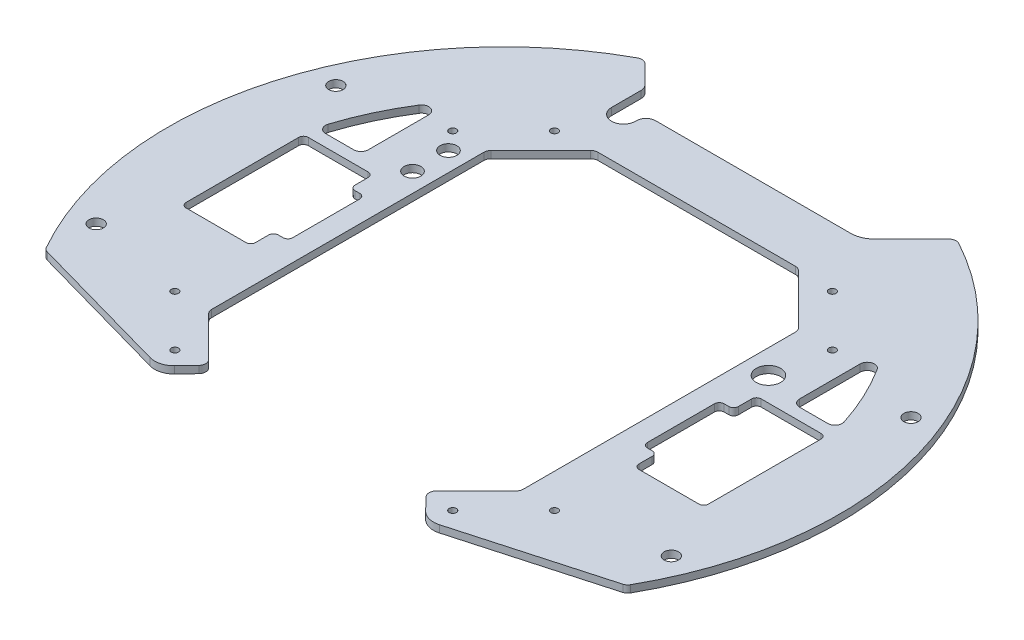
SolidWorks part; units mm, degrees
material "1060 Alloy"
ref_plane "Front Plane" through (0, 0, 0) normal (0, 0, 1) x (1, 0, 0)
ref_plane "Top Plane" through (0, 0, 0) normal (0, 1, 0) x (1, 0, 0)
ref_plane "Right Plane" through (0, 0, 0) normal (1, 0, 0) x (0, 0, -1)
sketch "Sketch1" plane through (0, 0, 0) normal (0, 1, 0) x (1, 0, 0)
  circle A0 centre (0, 0) radius 140
  dimension "D1" = 280
extrude "Boss-Extrude1" add sketch "Sketch1" along normal blind 3
sketch "Sketch17" plane through (0, 0, 0) normal (0, -1, 0) x (1, 0, 0)
  line L0 (-50, 90) -> (-121.2436, 70)
  line L1 (-50, 90) -> (50, 90)
  line L2 (-121.2436, 70) -> (-121.2436, 140)
  line L3 (-121.2436, 140) -> (121.2436, 140)
  line L4 (121.2436, 140) -> (121.2436, 70)
  line L5 (121.2436, 70) -> (50, 90)
  circle A0 centre (0, 0) radius 140 construction
  dimension "D1" = 90
  dimension "D2" = 50
  dimension "D3" = 50
  dimension "D4" = 70
extrude "Cut-Extrude1" cut sketch "Sketch17" against normal up to next
sketch "Sketch19" plane through (0, 3, 0) normal (0, 1, 0) x (1, 0, 0)
  line L0 (-68.5894, 68.5894) -> (68.5894, -68.5894) construction
  line L1 (97, 40.1787) -> (40.1787, 97) construction
  line L2 (40.1787, 97) -> (-40.1787, 97) construction
  line L3 (-40.1787, 97) -> (-97, 40.1787) construction
  line L4 (-97, 40.1787) -> (-97, -40.1787) construction
  line L5 (-97, -40.1787) -> (-40.1787, -97) construction
  line L6 (-40.1787, -97) -> (40.1787, -97) construction
  line L7 (40.1787, -97) -> (97, -40.1787) construction
  line L8 (97, -40.1787) -> (97, 40.1787) construction
  line L9 (68.5894, 68.5894) -> (-68.5894, -68.5894) construction
  circle A0 centre (-79.196, -57.9828) radius 1.5
  circle A1 centre (-79.196, 57.9828) radius 1.5
  circle A2 centre (79.196, 57.9828) radius 1.5
  circle A3 centre (79.196, -57.9828) radius 1.5
  circle A4 centre (0, 0) radius 97 construction
  circle A5 centre (-57.9828, -79.196) radius 1.5
  circle A6 centre (57.9828, 79.196) radius 1.5
  circle A7 centre (-57.9828, 79.196) radius 1.5
  circle A8 centre (57.9828, -79.196) radius 1.5
  dimension "D5" = 3
  dimension "D1" = 15
  dimension "D2" = 15
  dimension "D6" = 97
extrude "Cut-Extrude3" cut sketch "Sketch19" against normal up to next
sketch "Sketch20" plane through (0, 3, 0) normal (0, 1, 0) x (1, 0, 0)
  line L0 (-65, 123.996) -> (-45, 103.996)
  line L1 (-45, 103.996) -> (45, 103.996)
  line L2 (45, 103.996) -> (65, 123.996)
  arc A1 (121.2436, -70) -> (-121.2436, -70) centre (0, 0) ccw construction
  dimension "D1" = 130
  dimension "D2" = 90
  dimension "D3" = 45
extrude "Cut-Extrude4" cut sketch "Sketch20" against normal up to next
sketch "Sketch21" plane through (0, 3, 0) normal (0, 1, 0) x (1, 0, 0)
  line L0 (-42.4669, 80.5696) -> (0, 60)
  line L1 (0, 60) -> (42.4669, 80.5696)
  line L2 (59.9558, 63.0807) -> (40, 15)
  line L3 (40, 15) -> (61.3906, -61.646)
  line L4 (52.194, -84.7177) -> (0, -30) construction
  line L5 (0, -30) -> (-52.194, -84.7177) construction
  line L6 (-61.3906, -61.646) -> (-40, 15)
  line L7 (-40, 15) -> (-59.9558, 63.0807)
  line L8 (-59.9558, 63.0807) -> (-42.4669, 80.5696)
  line L9 (42.4669, 80.5696) -> (59.9558, 63.0807)
  line L10 (-45.4202, -77.6164) -> (-52.3849, -84.9179)
  line L12 (-68.5894, 68.5894) -> (68.5894, -68.5894) construction
  line L13 (97, 40.1787) -> (40.1787, 97) construction
  line L14 (40.1787, 97) -> (-40.1787, 97) construction
  line L15 (-40.1787, 97) -> (-97, 40.1787) construction
  line L16 (-97, 40.1787) -> (-97, -40.1787) construction
  line L17 (-97, -40.1787) -> (-40.1787, -97) construction
  line L18 (-40.1787, -97) -> (40.1787, -97) construction
  line L19 (40.1787, -97) -> (97, -40.1787) construction
  line L20 (97, -40.1787) -> (97, 40.1787) construction
  line L21 (68.5894, 68.5894) -> (-68.5894, -68.5894) construction
  line L22 (-45.4202, -77.6164) -> (-61.3906, -61.646)
  line L23 (-121.2436, -70) -> (-50, -90) construction
  line L24 (-60.336, -87.0984) -> (-50, -90)
  line L25 (45.4202, -77.6164) -> (61.3906, -61.646)
  line L26 (-59.9558, 63.0807) -> (-65.3716, 76.1292) construction
  line L27 (-54.4954, 86.3958) -> (-42.4669, 80.5696) construction
  line L28 (42.4669, 80.5696) -> (54.4954, 86.3958) construction
  line L29 (65.3716, 76.1292) -> (59.9558, 63.0807) construction
  line L30 (-50, -90) -> (50, -90)
  line L31 (50, -90) -> (60.336, -87.0984)
  line L32 (50, -90) -> (121.2436, -70) construction
  line L34 (52.3849, -84.9179) -> (45.4202, -77.6164)
  arc A0 (-65.3716, 76.1292) -> (-54.4954, 86.3958) centre (-57.9828, 79.196) cw construction
  arc A1 (54.4954, 86.3958) -> (65.3716, 76.1292) centre (57.9828, 79.196) cw construction
  arc A2 (-52.194, -84.7177) -> (-65.6416, -76.8845) centre (-57.9828, -79.196) cw construction
  arc A3 (65.6416, -76.8845) -> (52.194, -84.7177) centre (57.9828, -79.196) cw construction
  arc A4 (-52.3849, -84.9179) -> (-60.336, -87.0984) centre (-58.1737, -79.3962) cw
  circle A5 centre (0, 0) radius 97 construction
  arc A6 (52.3849, -84.9179) -> (60.336, -87.0984) centre (58.1737, -79.3962) ccw
  ellipse E0 centre (0, 15) end of major axis (0, 60) minor radius 40 construction
  dimension "D1" = 40
  dimension "D2" = 8
  dimension "D3" = 15
  dimension "D4" = 15
  dimension "D5" = 45
  dimension "D6" = 10
  dimension "D7" = 10
  dimension "D8" = 97
  dimension "D9" = 10
  dimension "D14" = 10
extrude "Cut-Extrude5" cut sketch "Sketch21" against normal up to next
fillet "Fillet1" radius 20 3 edges at (40, 1.5, -15) (-40, 1.5, -15) (0, 1.5, -60)
fillet "Fillet2" radius 10 2 edges at (45, 1.5, -103.996) (-45, 1.5, -103.996)
sketch "Sketch22" plane through (0, 3, 0) normal (0, 1, 0) x (1, 0, 0)
  line L1 (80, 25.5) -> (109, 25.5)
  line L2 (80, 25.5) -> (80, -25.5)
  line L3 (80, -25.5) -> (109, -25.5)
  line L4 (109, 25.5) -> (109, -25.5)
  line L5 (-109, 25.5) -> (-80, 25.5)
  line L6 (-109, 25.5) -> (-109, -25.5)
  line L7 (-109, -25.5) -> (-80, -25.5)
  line L8 (-80, 25.5) -> (-80, -25.5)
  dimension "D1" = 80
  dimension "D2" = 80
  dimension "D4" = 51
  dimension "D5" = 29
  dimension "D7" = 25.5
extrude "Cut-Extrude6" cut sketch "Sketch22" against normal up to next
sketch "Sketch31" plane through (0, 3, 0) normal (0, 1, 0) x (1, 0, 0)
  line L0 (-80, -25.5) -> (-80, 25.5) construction
  line L1 (-80, 16) -> (-74, 16)
  line L2 (-80, 16) -> (-80, -16)
  line L3 (-80, -16) -> (-74, -16)
  line L4 (-74, 16) -> (-74, -16)
  line L5 (80, 25.5) -> (80, -25.5) construction
  line L6 (80, 16) -> (74, 16)
  line L7 (80, 16) -> (80, -16)
  line L8 (80, -16) -> (74, -16)
  line L9 (74, 16) -> (74, -16)
  line L10 (-109, 25.5) -> (-109, -25.5) construction
  dimension "D1" = 32
  dimension "D2" = 35
  dimension "D3" = 16
extrude "Cut-Extrude15" cut sketch "Sketch31" against normal up to next
fillet "Fillet3" radius 2 16 edges at (109, 1.5, 25.5) (80, 1.5, 25.5) (80, 1.5, -25.5) (109, 1.5, -25.5) (-80, 1.5, 25.5) (-109, 1.5, 25.5) (-80, 1.5, -25.5) (-109, 1.5, -25.5) (80, 1.5, 16) (74, 1.5, 16) (74, 1.5, -16) (80, 1.5, -16) (-80, 1.5, 16) (-74, 1.5, 16) (-80, 1.5, -16) (-74, 1.5, -16)
sketch "Sketch23" plane through (0, 3, 0) normal (0, 1, 0) x (1, 0, 0)
  circle A0 centre (-120, 50) radius 3
  circle A1 centre (-120, -50) radius 3
  circle A2 centre (120, -50) radius 3
  circle A3 centre (120, 50) radius 3
  dimension "D1" = 6
  dimension "D2" = 120
  dimension "D3" = 120
  dimension "D4" = 50
  dimension "D5" = 50
extrude "Cut-Extrude7" cut sketch "Sketch23" against normal up to next
sketch "Sketch24" plane through (0, 3, 0) normal (0, 1, 0) x (1, 0, 0)
  line L0 (-90, 68.3301) -> (-90, 30.5)
  line L1 (-90, 30.5) -> (-108.806, 30.5)
  line L2 (-82, 25.5) -> (-107, 25.5) construction
  arc A0 (-108.806, 30.5) -> (-90, 68.3301) centre (0, 0) cw
  arc A2 (-65, 123.996) -> (-121.2436, -70) centre (0, 0) ccw construction
  dimension "D3" = 27
  dimension "D1" = 5
  dimension "D2" = 90
extrude "Cut-Extrude8" cut sketch "Sketch24" against normal up to next (3 mm away)
fillet "Fillet4" radius 3 3 edges at (-90, 1.5, -68.3301) (-90, 1.5, -30.5) (-108.806, 1.5, -30.5)
mirror "Mirror1" about plane through (0, 0, 0) normal (1, 0, 0) of "Fillet4", "Cut-Extrude8"
sketch "Sketch26" plane through (0, 3, 0) normal (0, 1, 0) x (1, 0, 0)
  line L0 (-59.9558, 63.0807) -> (-65, 58.0366)
  line L1 (-59.9558, 63.0807) -> (-42.65, 21.3847) construction
  line L2 (-65, 58.0366) -> (-65, -58.0366)
  line L3 (-65, -58.0366) -> (-61.3906, -61.646)
  line L5 (-59.9558, 63.0807) -> (59.9558, 63.0807)
  line L6 (42.65, 21.3847) -> (59.9558, 63.0807) construction
  line L7 (59.9558, 63.0807) -> (65, 58.0366)
  line L8 (65, 58.0366) -> (65, -58.0366)
  line L9 (65, -58.0366) -> (61.3906, -61.646)
  line L10 (61.3906, -61.646) -> (41.8582, 8.3417) construction
  line L11 (61.3906, -61.646) -> (-61.3906, -61.646)
  line L12 (-80, -23.5) -> (-80, -18) construction
  line L13 (-41.8582, 8.3417) -> (-61.3906, -61.646) construction
  line L14 (-61.3906, -61.646) -> (-45.4202, -77.6164) construction
  line L15 (-42.4669, 80.5696) -> (-59.9558, 63.0807) construction
  dimension "D1" = 15
extrude "Cut-Extrude10" cut sketch "Sketch26" against normal up to next
sketch "Sketch27" plane through (0, 3, 0) normal (0, 1, 0) x (1, 0, 0)
  line L0 (-42.4669, 80.5696) -> (-65, 58.0366) construction
  line L1 (-42.4669, 80.5696) -> (42.4669, 80.5696)
  line L2 (65, 58.0366) -> (42.4669, 80.5696) construction
  line L3 (-42.4669, 62.2226) -> (42.4669, 62.2226)
  line L5 (-8.7185, 64.223) -> (-42.4669, 80.5696) construction
  line L8 (-42.4669, 62.2226) -> (-42.4669, 80.5696)
  line L9 (42.4669, 62.2226) -> (42.4669, 80.5696)
  arc A0 (-8.7185, 64.223) -> (-5.7955, 63.0807) centre (0, 82.2226) ccw construction
extrude "Cut-Extrude11" cut sketch "Sketch27" against normal up to next
sketch "Sketch28" plane through (0, 3, 0) normal (0, 1, 0) x (1, 0, 0)
  line L0 (-49.55, 99.6) -> (-49.55, 119.6) construction
  line L1 (-54.55, 99.6) -> (-54.55, 119.6)
  line L2 (-44.55, 99.6) -> (-44.55, 119.6)
  arc A0 (-54.55, 99.6) -> (-44.55, 99.6) centre (-49.55, 99.6) ccw
  arc A1 (-44.55, 119.6) -> (-54.55, 119.6) centre (-49.55, 119.6) ccw
  point P2 (-49.55, 109.6)
  dimension "D1" = 5
  dimension "D2" = 49.55
  dimension "D3" = 99.6
  dimension "D4" = 20
extrude "Cut-Extrude12" cut sketch "Sketch28" against normal up to next
fillet "Fillet5" radius 3 12 edges at (-65, 1.5, -123.996) (65, 1.5, -123.996) (121.2436, 1.5, 70) (65, 1.5, 58.0366) (65, 1.5, -58.0366) (-65, 1.5, -58.0366) (-65, 1.5, 58.0366) (-121.2436, 1.5, 70) (45.4202, 1.5, 77.6164) (-45.4202, 1.5, 77.6164) (42.4669, 1.5, -80.5696) (-42.4669, 1.5, -80.5696)
fillet "Fillet6" radius 4 2 edges at (-44.55, 1.5, -104.7025) (-54.55, 1.5, -113.546)
sketch "Sketch29" plane through (0, 3, 0) normal (0, 1, 0) x (1, 0, 0)
  line L0 (65, -56.7939) -> (65, 56.7939) construction
  line L2 (104.7748, 30.5) -> (93, 30.5) construction
  circle A0 centre (75, 35.5) radius 5.1
  dimension "D1" = 10.2
  dimension "D2" = 10
  dimension "D3" = 5
extrude "Cut-Extrude13" cut sketch "Sketch29" against normal up to next
sketch "Sketch30" plane through (0, 3, 0) normal (0, 1, 0) x (1, 0, 0)
  line L1 (-65, 56.7939) -> (-65, -56.7939) construction
  circle A0 centre (-73, 50) radius 3.5
  circle A1 centre (-73, 35) radius 3.5
  dimension "D1" = 7
  dimension "D2" = 15
  dimension "D3" = 8
  dimension "D4" = 35
extrude "Cut-Extrude14" cut sketch "Sketch30" against normal up to next
equation "\"D3@Sketch20\" = \"D2@Sketch20\" / 2"
